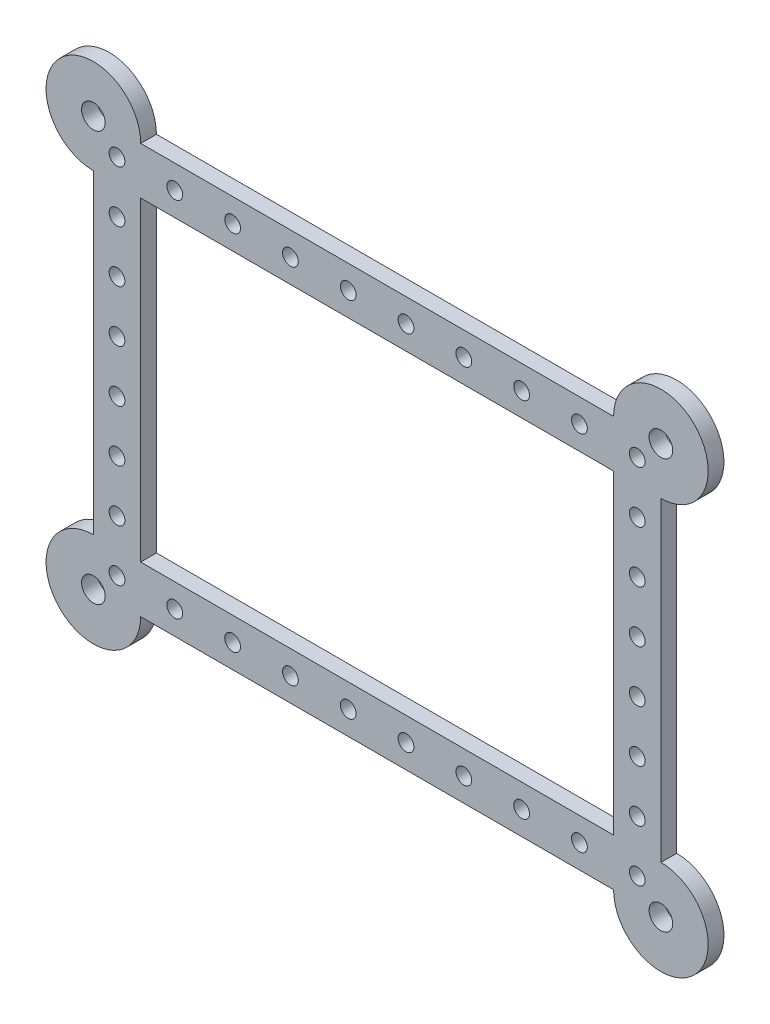
SolidWorks part; units mm, degrees
ref_plane "Front" through (0, 0, 0) normal (0, 0, 1) x (1, 0, 0)
ref_plane "Top" through (0, 0, 0) normal (0, 1, 0) x (1, 0, 0)
ref_plane "Right" through (0, 0, 0) normal (1, 0, 0) x (0, 0, -1)
sketch "Sketch1" plane through (0, 0, 0) normal (0, 0, 1) x (1, 0, 0)
  line L1 (0, 0) -> (120, 0)
  line L2 (0, 0) -> (0, 80)
  line L3 (0, 80) -> (120, 80)
  line L4 (120, 0) -> (120, 80)
  line L5 (0, -12) -> (120, -12)
  line L6 (-12, 0) -> (-12, 80)
  line L7 (0, 92) -> (120, 92)
  line L8 (132, 0) -> (132, 80)
  arc A0 (132, 80) -> (120, 92) centre (132, 92) ccw
  arc A1 (0, 92) -> (-12, 80) centre (-12, 92) ccw
  arc A2 (-12, 0) -> (0, -12) centre (-12, -12) ccw
  arc A3 (120, -12) -> (132, 0) centre (132, -12) ccw
  point P9 (0, 40)
  dimension "D1" = 120
  dimension "D2" = 80
  dimension "D3" = 12
  dimension "D4" = 12
  dimension "D5" = 12
  dimension "D6" = 12
extrude "Frame" add sketch "Sketch1" along normal blind 4
sketch "Centreline" plane through (0, 0, 0) normal (0, 0, -1) x (-1, 0, 0)
  line L0 (-132, 0) -> (-132, 80) construction
  line L1 (-126, 86) -> (6, 86)
  line L2 (-126, 86) -> (-126, -6)
  line L3 (-126, -6) -> (6, -6)
  line L4 (6, 86) -> (6, -6)
  line L5 (-120, 92) -> (0, 92) construction
  line L6 (12, 80) -> (12, 0) construction
  line L7 (0, -12) -> (-120, -12) construction
  dimension "D1" = 6
  dimension "D2" = 6
  dimension "D3" = 6
  dimension "D4" = 6
sketch "Sketch3" plane through (0, 0, 0) normal (0, 0, -1) x (-1, 0, 0)
  circle A0 centre (-126, 86) radius 2
extrude "Cut-Extrude1" cut sketch "Sketch3" against normal blind 4 contours A0
pattern_curve "CrvPattern2" of "Cut-Extrude1" parameters "D1"=10, "D3"=10, "D2"=1, "D4"=10
pattern_curve "CrvPattern3" of "Cut-Extrude1" parameters "D1"=8, "D3"=10, "D2"=1, "D4"=10
sketch "Sketch4" plane through (0, 0, 0) normal (0, 0, -1) x (-1, 0, 0)
  circle A0 centre (6, -6) radius 2
extrude "Cut-Extrude2" cut sketch "Sketch4" against normal blind 4 contours A0
pattern_curve "CrvPattern5" of "Cut-Extrude2" parameters "D1"=10, "D3"=10, "D2"=1, "D4"=10
pattern_curve "CrvPattern6" of "Cut-Extrude2" parameters "D1"=8, "D3"=10, "D2"=1, "D4"=10
sketch "Sketch12" plane through (0, 0, 0) normal (0, 0, -1) x (-1, 0, 0)
  circle A0 centre (-132, 92) radius 3
  circle A1 centre (12, 92) radius 3
  circle A2 centre (12, -12) radius 3
  circle A3 centre (-132, -12) radius 3
  dimension "D1" = 6
extrude "Cut-Extrude4" cut sketch "Sketch12" against normal blind 10
